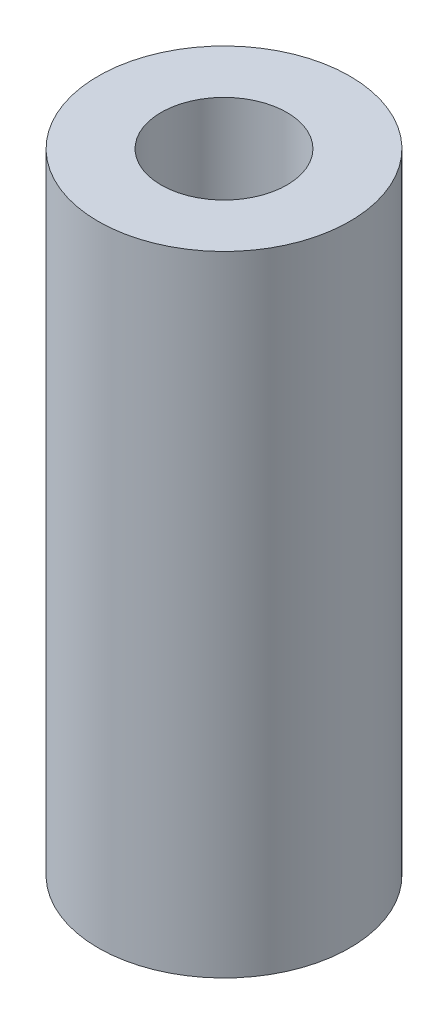
SolidWorks part; units mm, degrees
other "Markup1"
sketch "Sketch2" plane through (7, 40, 7) normal (0.4293, 0.7189, 0.5467) x (0.8301, -0.0756, -0.5525)
ref_plane "Front Plane" through (0, 0, 0) normal (0, 0, 1) x (1, 0, 0)
ref_plane "Top Plane" through (0, 0, 0) normal (0, 1, 0) x (1, 0, 0)
ref_plane "Right Plane" through (0, 0, 0) normal (1, 0, 0) x (0, 0, -1)
sketch "Sketch1" plane through (0, 0, 0) normal (0, 1, 0) x (1, 0, 0)
  line L0 (-921.3731, 0) -> (45147.2843, 0) construction
  line L1 (0, -921.3731) -> (0, 45147.2843) construction
  circle A0 centre (0, 0) radius 7
  circle A1 centre (0, 0) radius 3.5
  dimension "D1" = 14
  dimension "D2" = 7
extrude "Boss-Extrude1" add sketch "Sketch1" along normal blind 35
